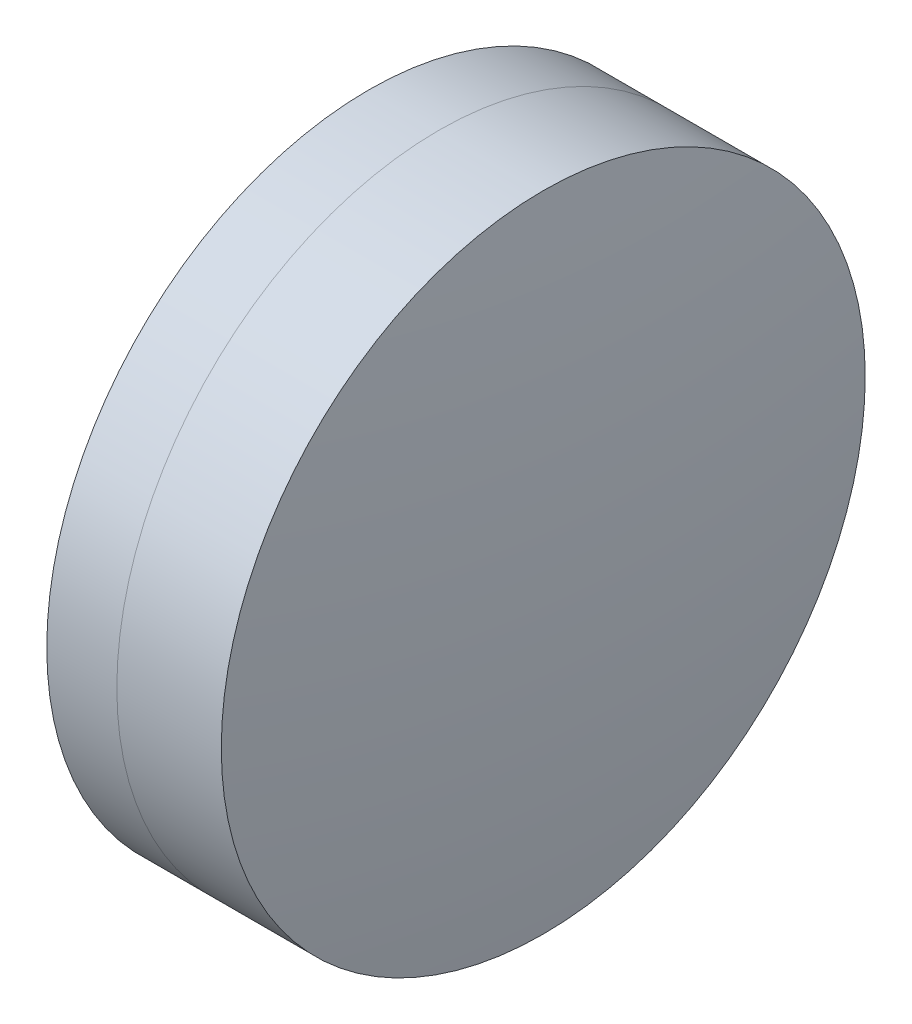
SolidWorks part; units mm, degrees
ref_plane "前视基准面" through (0, 0, 0) normal (0, 0, 1) x (1, 0, 0)
ref_plane "上视基准面" through (0, 0, 0) normal (0, 1, 0) x (1, 0, 0)
ref_plane "右视基准面" through (0, 0, 0) normal (1, 0, 0) x (0, 0, -1)
sketch "草图1" plane through (0, 0, 0) normal (0, 1, 0) x (1, 0, 0)
  line L0 (161.8332, 0) -> (266.0476, 0) construction
  line L1 (239.7638, -12.7) -> (242.527, -12.7)
  line L2 (239.7638, 12.7) -> (242.527, 12.7)
  arc A0 (242.527, -12.7) -> (242.527, 12.7) centre (211.0958, 0) ccw
  arc A1 (239.7638, 12.7) -> (239.7638, -12.7) centre (284.4958, 0) ccw
  point P10 (237.9958, 0)
  point P11 (244.9958, 0)
  dimension "D3" = 46.5
  dimension "D4" = 33.9
  dimension "D1" = 12.7
  dimension "D2" = 12.7
  dimension "D5" = 7
revolve "旋转1" add sketch "草图1" angle 360 about L0
sketch "草图2" plane through (0, 0, 0) normal (0, 1, 0) x (1, 0, 0)
  line L0 (-0.5519, 0) -> (253.9868, 0) construction
  line L2 (242.527, 12.7) -> (246.6476, 12.7)
  line L3 (242.527, -12.7) -> (246.6476, -12.7)
  arc A0 (246.6476, -12.7) -> (246.6476, 12.7) centre (151.9958, 0) ccw
  arc A1 (242.527, -12.7) -> (242.527, 12.7) centre (211.0958, 0) ccw construction
  arc A2 (242.527, -12.7) -> (242.527, 12.7) centre (211.0958, 0) ccw
  point P4 (244.9958, 0)
  point P8 (247.4958, 0)
  dimension "D1" = 95.5
  dimension "D2" = 2.5
revolve "旋转3" add sketch "草图2" angle 360 about L0
